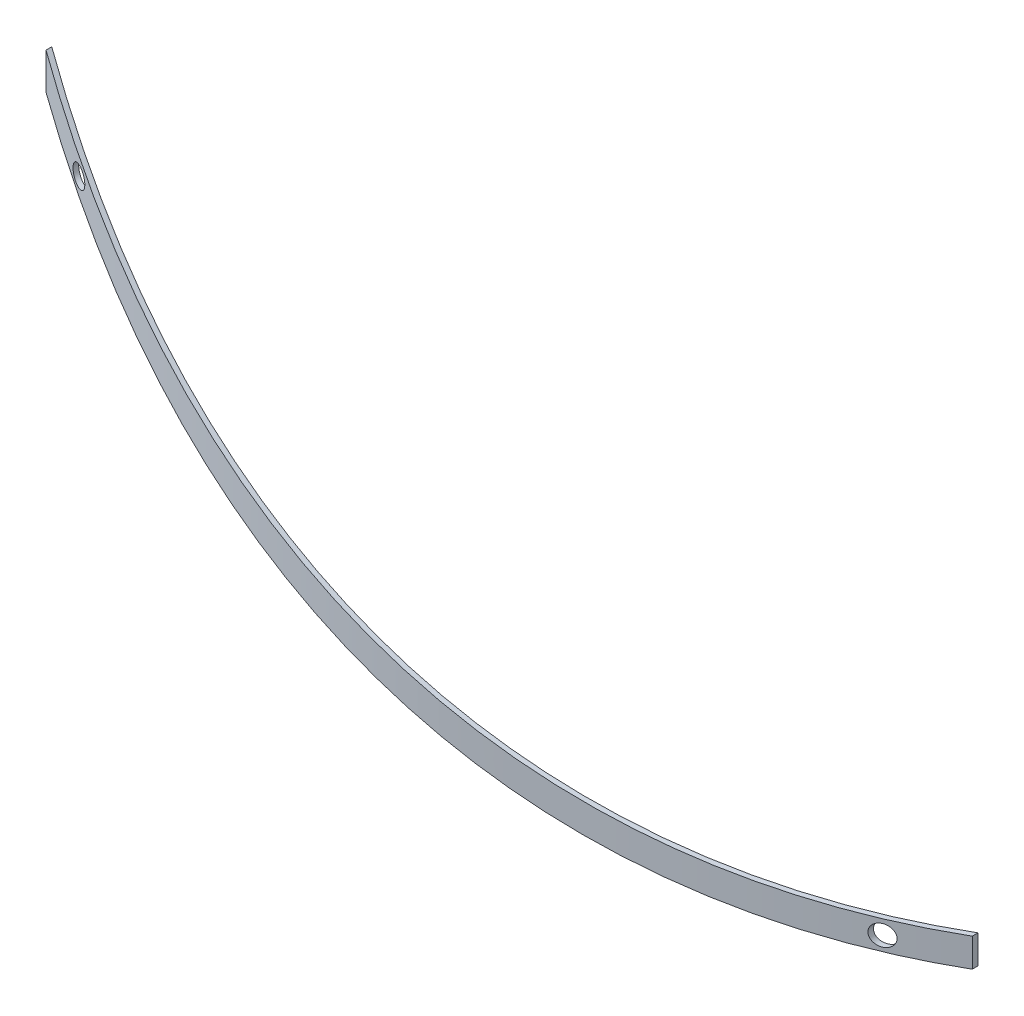
SolidWorks part; units mm, degrees
material "6063-O"
ref_plane "Front Plane" through (0, 0, 0) normal (0, 0, 1) x (1, 0, 0)
ref_plane "Top Plane" through (0, 0, 0) normal (0, 1, 0) x (1, 0, 0)
ref_plane "Right Plane" through (0, 0, 0) normal (1, 0, 0) x (0, 0, -1)
sketch "Sketch2" plane through (0, 0, 0) normal (0, 1, 0) x (1, 0, 0)
  line L0 (3714.5722, -2111.7614) -> (3714.5722, -2139.7857)
  line L1 (-815.4278, -2111.7614) -> (-815.4278, -2139.7857)
  arc A0 (3714.5722, -2139.7857) -> (-815.4278, -2139.7857) centre (1449.5722, 2345.7911) cw
  arc A1 (3714.5722, -2111.7614) -> (-815.4278, -2111.7614) centre (1449.5722, 2345.7911) cw
extrude "Boss-Extrude1" add sketch "Sketch2" along normal blind 3000
sketch "Sketch3" plane through (0, 0, 0) normal (0, 0, 1) x (1, 0, 0)
  line L0 (-815.4278, 2495.9061) -> (-815.4278, 2674.673)
  line L1 (-815.4278, 3000) -> (-815.4278, 0) construction
  line L2 (3714.5722, 1046.5696) -> (3714.5722, 1186.7059)
  line L4 (3714.5722, 3000) -> (3714.5722, 0) construction
  circle A0 centre (-515.4278, 2360.0191) radius 50
  circle A1 centre (3414.5722, 1110.0191) radius 50
  arc A2 (-815.4278, 2674.673) -> (3714.5722, 1186.7059) centre (3414.5722, 7912.9791) ccw
  arc A3 (-815.4278, 2495.9061) -> (3714.5722, 1046.5696) centre (3414.5722, 7912.9791) ccw
extrude "Cut-Extrude1" cut sketch "Sketch3" along normal blind 3000 flip side to cut
